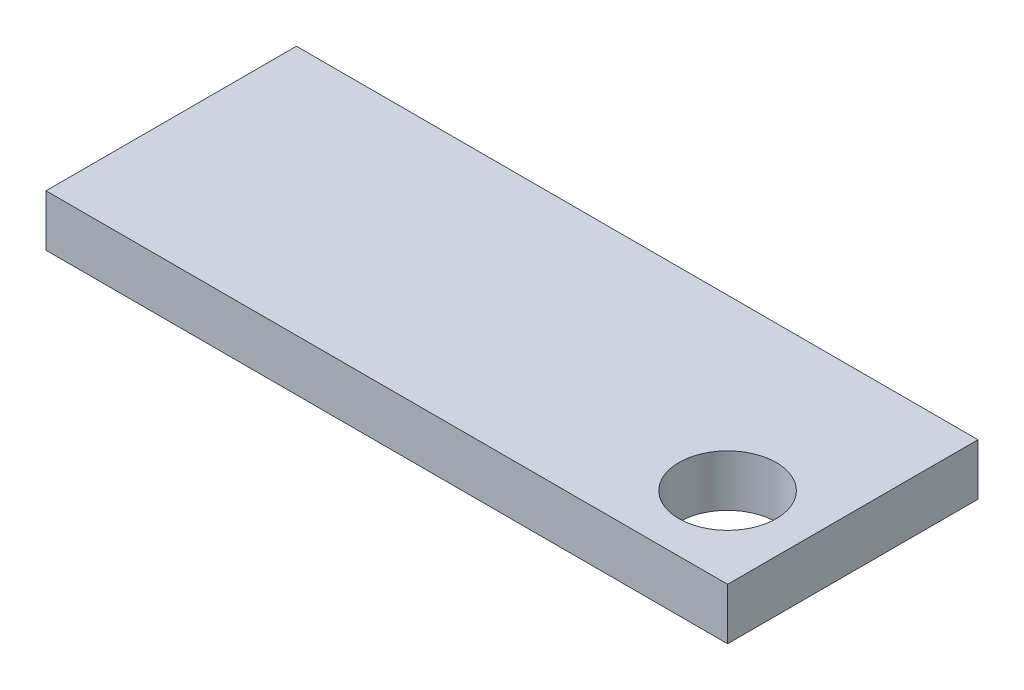
SolidWorks part; units mm, degrees
ref_plane "Front Plane" through (0, 0, 0) normal (0, 0, 1) x (1, 0, 0)
ref_plane "Top Plane" through (0, 0, 0) normal (0, 1, 0) x (1, 0, 0)
ref_plane "Right Plane" through (0, 0, 0) normal (1, 0, 0) x (0, 0, -1)
sketch "Sketch1" plane through (0, 0, 0) normal (0, 1, 0) x (1, 0, 0)
  line L1 (0, 0) -> (42, 0)
  line L2 (0, 0) -> (0, 15.43)
  line L3 (0, 15.43) -> (42, 15.43)
  line L4 (42, 0) -> (42, 15.43)
  dimension "D1" = 42
  dimension "D2" = 15.43
extrude "Boss-Extrude1" add sketch "Sketch1" along normal mid plane 3.175
sketch "Sketch2" plane through (0, 1.5875, 0) normal (0, 1, 0) x (1, 0, 0)
  line L0 (0, 15.43) -> (0, 0) construction
  line L2 (0, 0) -> (42, 0) construction
  circle A0 centre (37, 5) radius 3
  point P0 (37, 5)
  point P9 (37, 5)
  dimension "D2" = 6
  dimension "D1" = 40
  dimension "D3" = 5
hole_wizard "Ø6.0mm Dowel Hole1" positions "Sketch2" profile "Sketch4" hole size "Ø6.0" standard "ANSI Metric" end condition through all
sketch "Sketch4" plane through (37, 1.5875, -5) normal (1, 0, 0) x (0, 0, 1)
  line L0 (0, 0) -> (0, 3.175)
  line L1 (0, 3.175) -> (3, 3.175)
  line L2 (3, 3.175) -> (3, 0)
  line L5 (3, 0) -> (0, 0)
  line L11 (0, -6.35) -> (0, 107.95) construction
  dimension "Thru Hole Dia." = 6
  dimension "Thru Hole Depth" = 3.175
